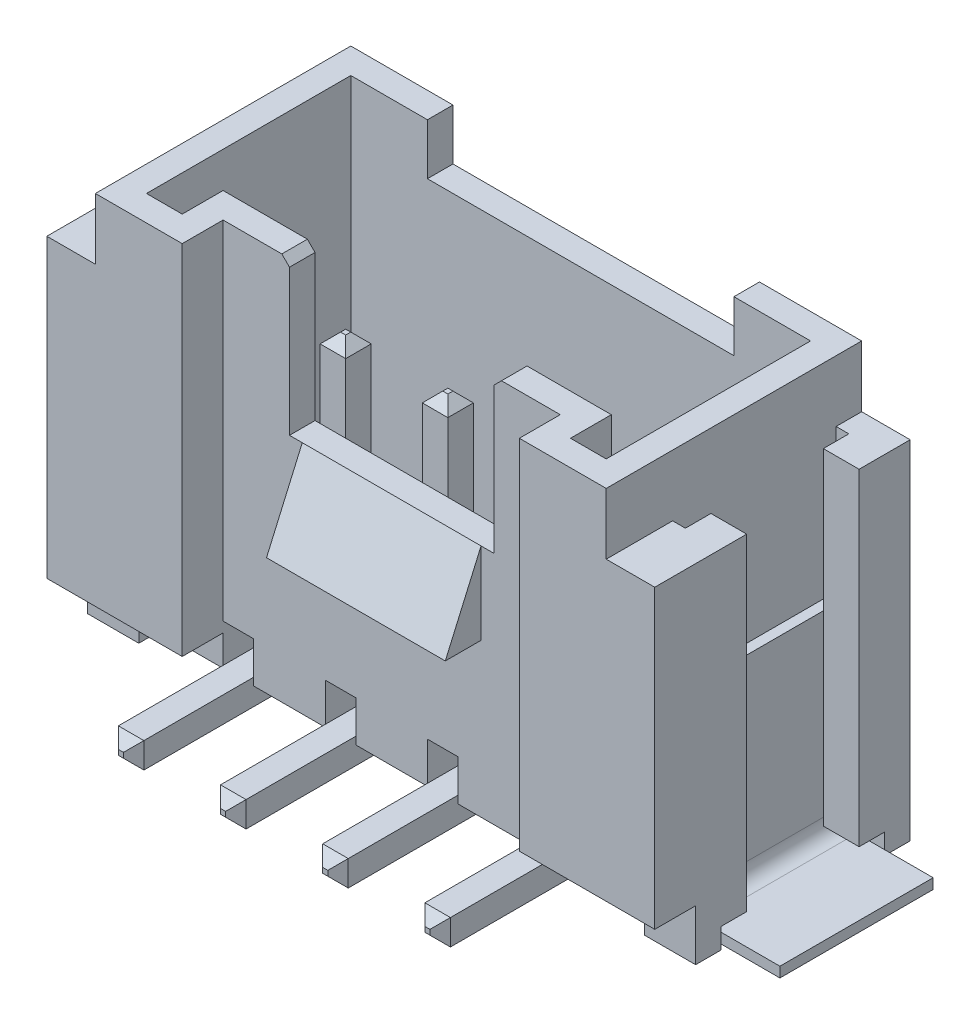
SolidWorks part; units mm, degrees
material "ABS"
ref_plane "Plan de face" through (0, 0, 0) normal (0, 0, 1) x (1, 0, 0)
ref_plane "Plan de dessus" through (0, 0, 0) normal (0, 1, 0) x (1, 0, 0)
ref_plane "Plan de droite" through (0, 0, 0) normal (1, 0, 0) x (0, 0, -1)
sketch "Esquisse1" plane through (0, 0, 0) normal (0, 1, 0) x (1, 0, 0)
  line L1 (-5, 0) -> (5, 0)
  line L2 (-5, 0) -> (-5, 5)
  line L3 (-5, 5) -> (5, 5)
  line L4 (5, 0) -> (5, 5)
  dimension "D1" = 10
  dimension "D2" = 5
extrude "Boss.-Extru.1" add sketch "Esquisse1" along normal blind 8
sketch "Esquisse2" plane through (0, 8, 0) normal (0, 1, 0) x (1, 0, 0)
  line L0 (-5, 0) -> (5, 0) construction
  line L1 (-3.3, -0.8) -> (3.3, -0.8)
  line L2 (-3.3, -0.8) -> (-3.3, 0.8)
  line L3 (-3.3, 0.8) -> (3.3, 0.8)
  line L4 (3.3, -0.8) -> (3.3, 0.8)
  line L5 (-3.3, -0.8) -> (3.3, 0.8) construction
  line L6 (-3.3, 0.8) -> (3.3, -0.8) construction
  line L7 (5, 0) -> (5, 5) construction
  point P0 (0, 0)
  dimension "D1" = 0.8
  dimension "D2" = 1.7
extrude "Enlèv. mat.-Extru.1" cut sketch "Esquisse2" against normal through all
sketch "Esquisse4" plane through (0, 8, 0) normal (0, 1, 0) x (1, 0, 0)
  line L16 (-3.8, 1.3) -> (3.8, 1.3)
  line L17 (3.8, 1.3) -> (3.8, 0.5)
  line L18 (3.8, 0.5) -> (4.5, 0.5)
  line L19 (4.5, 0.5) -> (4.5, 4.5)
  line L20 (4.5, 4.5) -> (-4.5, 4.5)
  line L21 (-4.5, 4.5) -> (-4.5, 0.5)
  line L22 (-4.5, 0.5) -> (-3.8, 0.5)
  line L23 (-3.8, 0.5) -> (-3.8, 1.3)
  line L24 (-3.8, 1.3) -> (3.8, 1.3)
  line L25 (3.8, 1.3) -> (3.8, 0.5)
  line L26 (3.8, 0.5) -> (4.5, 0.5)
  line L27 (4.5, 0.5) -> (4.5, 4.5)
  line L28 (4.5, 4.5) -> (-4.5, 4.5)
  line L29 (-4.5, 4.5) -> (-4.5, 0.5)
  line L30 (-4.5, 0.5) -> (-3.8, 0.5)
  line L31 (-3.8, 0.5) -> (-3.8, 1.3)
  dimension "D1" = 0.5
extrude "Enlèv. mat.-Extru.2" cut sketch "Esquisse4" against normal blind 6.5
sketch "Esquisse17" plane through (0, 8, 0) normal (0, 1, 0) x (1, 0, 0)
  line L0 (5, 0) -> (5, 5) construction
  line L1 (5, 5) -> (5.95, 5)
  line L2 (5, 5) -> (5, 0)
  line L3 (5, 0) -> (5.95, 0)
  line L4 (5.95, 5) -> (5.95, 0)
  line L5 (5, 5) -> (-5, 5) construction
  line L6 (5, 4.5) -> (5.25, 4.5)
  line L7 (5.25, 4.5) -> (5.25, 4)
  line L8 (5.25, 4) -> (5.95, 4)
  line L9 (5, 2.9) -> (5.95, 2.9) construction
  line L10 (5.25, 1.8) -> (5.95, 1.8)
  line L11 (5.25, 1.3) -> (5.25, 1.8)
  line L12 (5, 1.3) -> (5.25, 1.3)
  line L13 (5.95, 4) -> (5.95, 1.8)
  line L14 (5, 1.3) -> (5, 4.5)
  line M12 (5, 0) -> (5, 5)
  dimension "D1" = 5.95
  dimension "D2" = 2.2
  dimension "D3" = 3.2
  dimension "D4" = 1
  dimension "D5" = 0.25
extrude "Boss.-Extru.3" add sketch "Esquisse17" against normal up to surface (6.8 mm away) from offset 1.2 contours L7 L8 L4 L1 L2 L6 | L12 L3 L4 L10 L11 M12 up to face at (0, 0, -1.45) offset against normal yes
mirror "Symétrie3" about plane through (0, 0, 0) normal (1, 0, 0) of "Boss.-Extru.3"
sketch "Esquisse5" plane through (0, 8, 0) normal (0, 1, 0) x (1, 0, 0)
  line L0 (4.5, 4.5) -> (-4.5, 4.5) construction
  line L1 (-3, 4) -> (3, 4)
  line L2 (-3, 4) -> (-3, 5)
  line L3 (-3, 5) -> (3, 5)
  line L4 (3, 4) -> (3, 5)
  line L5 (-3, 4) -> (3, 5) construction
  line L6 (-3, 5) -> (3, 4) construction
  line L7 (5, 5) -> (-5, 5) construction
  line L8 (5, 0) -> (5, 5) construction
  point P0 (0, 4.5)
  dimension "D1" = 2
extrude "Enlèv. mat.-Extru.3" cut sketch "Esquisse5" against normal blind 1
sketch "Esquisse6" plane through (0, 8, 0) normal (0, 1, 0) x (1, 0, 0)
  line L0 (3.3, 0.8) -> (-3.3, 0.8) construction
  line L1 (-2, 0.3) -> (2, 0.3)
  line L2 (-2, 0.3) -> (-2, 1.3)
  line L3 (-2, 1.3) -> (2, 1.3)
  line L4 (2, 0.3) -> (2, 1.3)
  line L5 (-2, 0.3) -> (2, 1.3) construction
  line L6 (-2, 1.3) -> (2, 0.3) construction
  line L7 (-3.8, 1.3) -> (3.8, 1.3) construction
  line L8 (5, 0) -> (5, 5) construction
  point P0 (0, 0.8)
  dimension "D1" = 3
extrude "Enlèv. mat.-Extru.4" cut sketch "Esquisse6" against normal blind 3
sketch "Esquisse7" plane through (5.95, 0, 0) normal (1, 0, 0) x (0, 0, -1)
  line L0 (0, 0) -> (0, 6.8) construction
  line L1 (0, 1) -> (0.8, 1)
  line L2 (0, 1) -> (0, 0)
  line L3 (0, 0) -> (0.8, 0)
  line L4 (0.8, 1) -> (0.8, 0)
  line L5 (1.8, 0) -> (0, 0) construction
  dimension "D1" = 1
  dimension "D2" = 0.8
extrude "Enlèv. mat.-Extru.5" cut sketch "Esquisse7" against normal through all
sketch "Esquisse11" plane through (0, 0, 0) normal (1, 0, 0) x (0, 0, -1)
  line L0 (0.8, 5) -> (0.1, 3.4)
  line L1 (0.8, 5) -> (0.8, 8) construction
  line L2 (1.3, 5) -> (0.8, 5) construction
  line L3 (0.1, 3.4) -> (0.8, 3.4)
  line L4 (0.8, 1) -> (0.8, 8) construction
  line L5 (0.8, 3.4) -> (0.8, 5)
  dimension "D1" = 0.7
  dimension "D2" = 1.6
extrude "Boss.-Extru.2" add sketch "Esquisse11" along normal mid plane 3.5
sketch "Esquisse18" plane through (0, 0, -0.8) normal (0, 0, 1) x (1, 0, 0)
  line L0 (5.95, 0) -> (-5.95, 0) construction
  line L1 (-4.95, -0.4) -> (4.95, -0.4)
  line L2 (-4.95, -0.4) -> (-4.95, 0.4)
  line L3 (-4.95, 0.4) -> (4.95, 0.4)
  line L4 (4.95, -0.4) -> (4.95, 0.4)
  line L5 (-4.95, -0.4) -> (4.95, 0.4) construction
  line L6 (-4.95, 0.4) -> (4.95, -0.4) construction
  line L7 (5.95, 0) -> (5.95, 1) construction
  line L9 (2.7, -0.4) -> (3.3, -0.4)
  line L10 (2.7, -0.4) -> (2.7, 1.2)
  line L11 (2.7, 1.2) -> (3.3, 1.2)
  line L12 (3.3, -0.4) -> (3.3, 1.2)
  line L13 (2.7, -0.4) -> (3.3, 1.2) construction
  line L14 (2.7, 1.2) -> (3.3, -0.4) construction
  line L15 (0.7, -0.4) -> (1.3, -0.4)
  line L16 (0.7, -0.4) -> (0.7, 1.2)
  line L17 (0.7, 1.2) -> (1.3, 1.2)
  line L18 (1.3, -0.4) -> (1.3, 1.2)
  line L19 (0.7, -0.4) -> (1.3, 1.2) construction
  line L20 (0.7, 1.2) -> (1.3, -0.4) construction
  line L21 (-1.3, -0.4) -> (-0.7, -0.4)
  line L22 (-1.3, -0.4) -> (-1.3, 1.2)
  line L23 (-1.3, 1.2) -> (-0.7, 1.2)
  line L24 (-0.7, -0.4) -> (-0.7, 1.2)
  line L25 (-1.3, -0.4) -> (-0.7, 1.2) construction
  line L26 (-1.3, 1.2) -> (-0.7, -0.4) construction
  line L27 (-3.3, -0.4) -> (-2.7, -0.4)
  line L28 (-3.3, -0.4) -> (-3.3, 1.2)
  line L29 (-3.3, 1.2) -> (-2.7, 1.2)
  line L30 (-2.7, -0.4) -> (-2.7, 1.2)
  line L31 (-3.3, -0.4) -> (-2.7, 1.2) construction
  line L32 (-3.3, 1.2) -> (-2.7, -0.4) construction
  point P0 (0, 0)
  point P10 (3, 0.4)
  point P15 (1, 0.4)
  point P20 (-1, 0.4)
  point P25 (-3, 0.4)
  line M7 (-3.3, 8) -> (-3.3, 1)
  line M13 (3.3, 1) -> (3.3, 8)
  dimension "D1" = 0.4
  dimension "D2" = 1
  dimension "D3" = 2
  dimension "D4" = 1
  dimension "D5" = 2
  dimension "D6" = 2
  dimension "D7" = 1.2
  dimension "D8" = 0.6
extrude "Enlèv. mat.-Extru.6" cut sketch "Esquisse18" against normal through all contours L3 L30 L29 L28 M7 | L3 L24 L23 L22 | L3 L18 L17 L16 | L3 L12 L11 L10 M13
sketch "Esquisse20" plane through (5.25, 0, 0) normal (-1, 0, 0) x (0, 0, 1)
  line L0 (-4.5, 0) -> (-4, 0) construction
  line L1 (-4.5, 0) -> (-1.3, 0)
  line L2 (-4.5, 0) -> (-4.5, 0.4)
  line L3 (-4.5, 0.4) -> (-1.3, 0.4)
  line L4 (-1.3, 0) -> (-1.3, 0.4)
  line L5 (-1.3, 0) -> (-1.3, 6.8) construction
  line L6 (-4.5, 0.4) -> (-1.3, 0.4) construction
extrude "Enlèv. mat.-Extru.7" cut sketch "Esquisse20" against normal through all and the other way through all
chamfer "Chanfrein1" distance 0.15 angle 45 2 edges at (2, 8, -1.05) (-2, 8, -1.05)
ref_plane "Plan1" through (3, 0, 0) normal (1, 0, 0) x (0, 0, -1)
sketch "Esquisse21" plane through (3, 0, 0) normal (1, 0, 0) x (0, 0, -1)
  line L0 (2.9, 5.2) -> (2.9, 0.75)
  line L1 (2.4, 0.25) -> (-1.5, 0.25)
  line L2 (4.5, 8) -> (0.5, 8) construction
  line L3 (1.3, 0) -> (0.8, 0) construction
  line L4 (4.5, 1.5) -> (4.5, 8) construction
  arc A0 (2.9, 0.75) -> (2.4, 0.25) centre (2.4, 0.75) cw
  dimension "D3" = 0.5
  dimension "D1" = 6.5
  dimension "D2" = 2.8
  dimension "D4" = 0.25
  dimension "D5" = 1.6
extrude "Extru.-Mince1" add sketch "Esquisse21" along normal mid plane 0.5 separate body thin thin type mid plane wall 0.5
chamfer "Chanfrein2" distance 0.2 angle 45 8 edges at (3, 0.5, 1.5) (3.25, 0.25, 1.5) (3, 0, 1.5) (2.75, 0.25, 1.5) (3, 5.2, -3.15) (3.25, 5.2, -2.9) (3, 5.2, -2.65) (2.75, 5.2, -2.9)
pattern_linear "Répétition linéaire1" count 4 spacing 2 along (-1, 0, 0) of "Extru.-Mince1", "Chanfrein2"
sketch "Esquisse22" plane through (0, 0, -1.3) normal (0, 0, -1) x (-1, 0, 0)
  line L0 (-5, 4) -> (-5, 0.5)
  line L1 (-5, 0.4) -> (-5, 6.8) construction
  line L2 (-5.5, 0) -> (-7, 0)
  line L4 (-5, 8) -> (-3, 8) construction
  arc A0 (-5, 0.5) -> (-5.5, 0) centre (-5.5, 0.5) cw
  point P13 (-4.95, 0)
  dimension "D3" = 0.5
  dimension "D1" = 1.5
  dimension "D2" = 4
extrude "Extru.-Mince2" add sketch "Esquisse22" along normal blind 3 from offset 0.1 separate body thin
mirror "Symétrie4" about plane through (0, 0, 0) normal (1, 0, 0) of bodies 122
